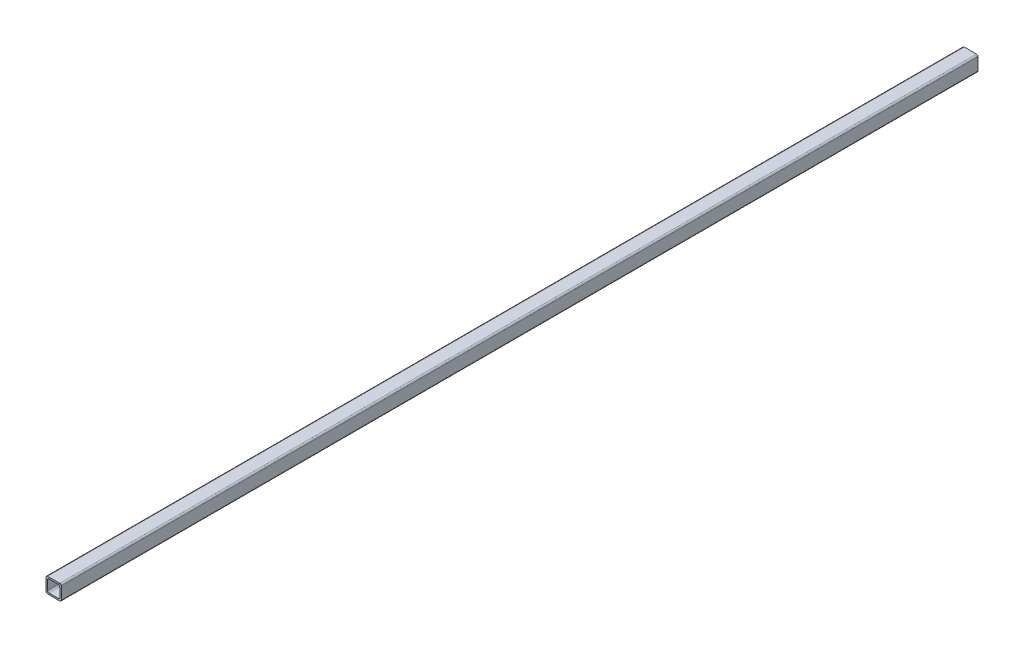
SolidWorks part; units mm, degrees
ref_plane "Front Plane" through (0, 0, 0) normal (0, 0, 1) x (1, 0, 0)
ref_plane "Top Plane" through (0, 0, 0) normal (0, 1, 0) x (1, 0, 0)
ref_plane "Right Plane" through (0, 0, 0) normal (1, 0, 0) x (0, 0, -1)
sketch "Sketch1" plane through (0, 0, 0) normal (0, 0, 1) x (1, 0, 0)
  line L1 (-7.8796, 6.7147) -> (2.1204, 6.7147)
  line L2 (-7.8796, 6.7147) -> (-7.8796, -3.2853)
  line L3 (-7.8796, -3.2853) -> (2.1204, -3.2853)
  line L4 (2.1204, 6.7147) -> (2.1204, -3.2853)
  line L5 (-7.8796, 6.7147) -> (2.1204, -3.2853) construction
  line L6 (-7.8796, -3.2853) -> (2.1204, 6.7147) construction
  line L7 (-6.8796, 5.7147) -> (1.1204, 5.7147)
  line L8 (-6.8796, 5.7147) -> (-6.8796, -2.2853)
  line L9 (-6.8796, -2.2853) -> (1.1204, -2.2853)
  line L10 (1.1204, 5.7147) -> (1.1204, -2.2853)
  line L11 (-6.8796, 5.7147) -> (1.1204, -2.2853) construction
  line L12 (-6.8796, -2.2853) -> (1.1204, 5.7147) construction
  point P0 (-2.8796, 1.7147)
  point P5 (-2.8796, 1.7147)
  dimension "D1" = 10
  dimension "D2" = 10
  dimension "D3" = 8
  dimension "D4" = 8
extrude "Boss-Extrude1" add sketch "Sketch1" along normal blind 600
fillet "Fillet1" radius 1 4 edges at (-6.8796, -2.2853, 300) (2.1204, -3.2853, 300) (2.1204, 6.7147, 300) (-7.8796, 6.7147, 300)
fillet "Fillet2" radius 1 4 edges at (-6.8796, 5.7147, 300) (1.1204, 5.7147, 300) (1.1204, -2.2853, 300) (-7.8796, -3.2853, 300)
